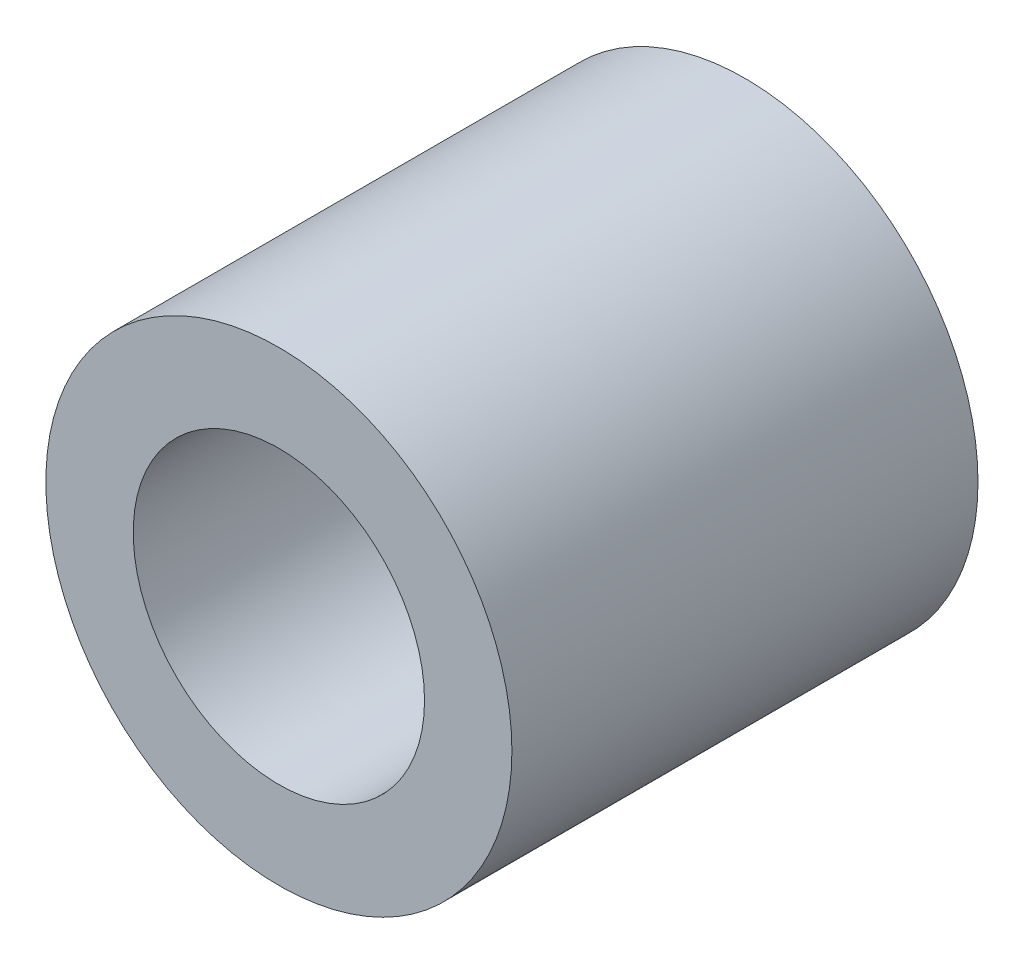
SolidWorks part; units mm, degrees
material "3.0255 (EN-AW 1350A)"
ref_plane "Plan de face" through (0, 0, 0) normal (0, 0, 1) x (1, 0, 0)
ref_plane "Plan de dessus" through (0, 0, 0) normal (0, 1, 0) x (1, 0, 0)
ref_plane "Plan de droite" through (0, 0, 0) normal (1, 0, 0) x (0, 0, -1)
sketch "Esquisse1" plane through (0, 0, 0) normal (0, 0, 1) x (1, 0, 0)
  circle A0 centre (0, 0) radius 5
  circle A1 centre (0, 0) radius 8
  dimension "D1" = 10
  dimension "D2" = 16
extrude "Boss.-Extru.1" add sketch "Esquisse1" along normal blind 16
